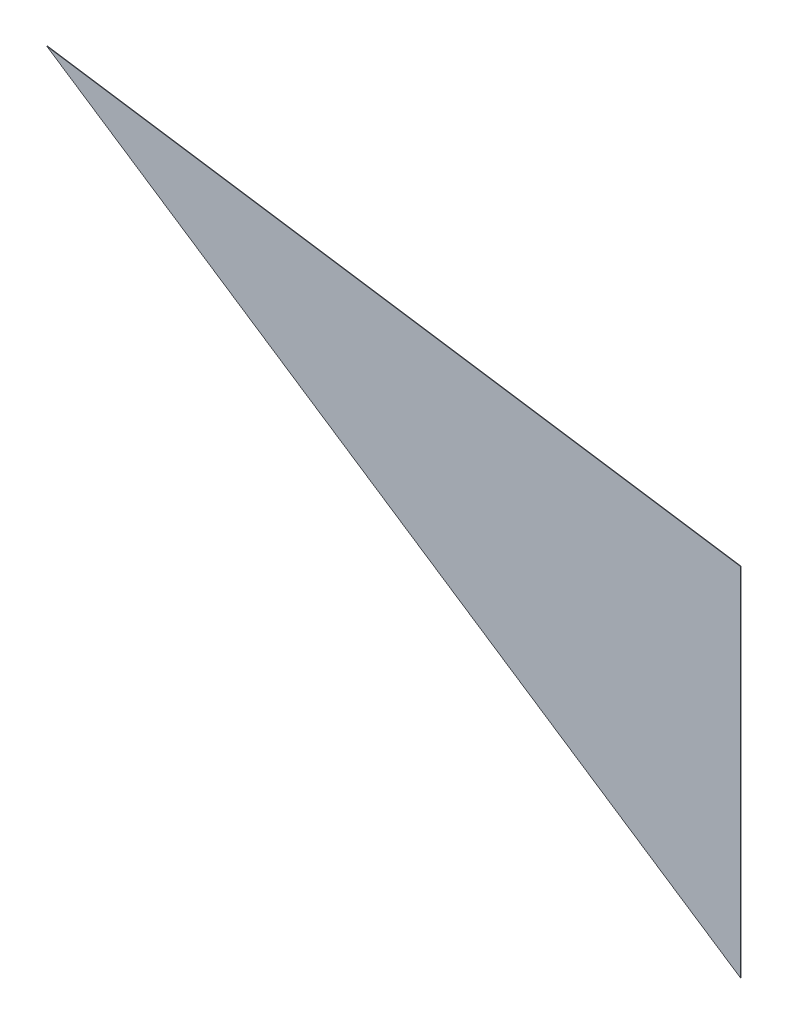
SolidWorks part; units mm, degrees
material "Hexcel AS4C (3000 Filamentów)"
ref_plane "Front Plane" through (0, 0, 0) normal (0, 0, 1) x (1, 0, 0)
ref_plane "Top Plane" through (0, 0, 0) normal (0, 1, 0) x (1, 0, 0)
ref_plane "Right Plane" through (0, 0, 0) normal (1, 0, 0) x (0, 0, -1)
sketch "Szkic1" plane through (0, 0, 0) normal (0, 0, 1) x (1, 0, 0)
  line L6 (-210.6801, 173.3732) -> (-210.6801, -159.8256)
  line L7 (-210.6801, -159.8256) -> (-859.317, 270.3406)
  line L8 (-210.6801, 173.3732) -> (-859.317, 270.3406)
extrude "Dodanie-wyciągnięcie1" add sketch "Szkic1" along normal blind 0.5
